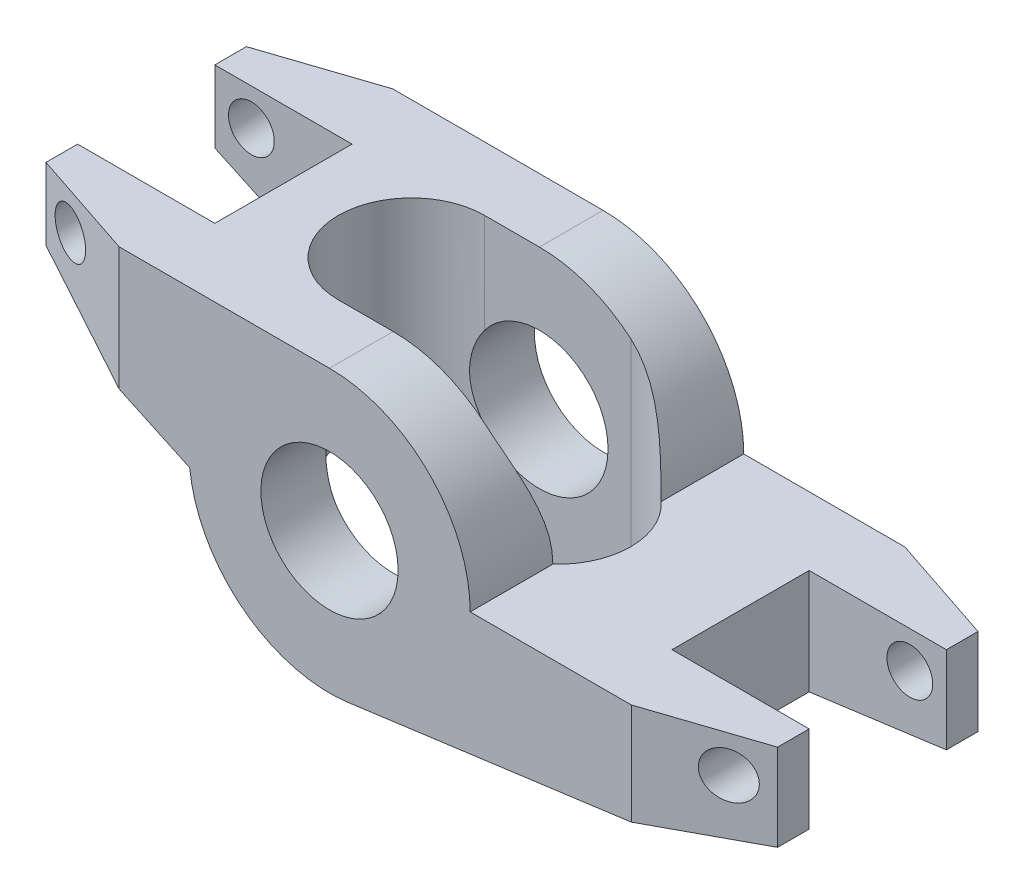
SolidWorks part; units mm, degrees
ref_plane "Front Plane" through (0, 0, 0) normal (0, 0, 1) x (1, 0, 0)
ref_plane "Top Plane" through (0, 0, 0) normal (0, 1, 0) x (1, 0, 0)
ref_plane "Right Plane" through (0, 0, 0) normal (1, 0, 0) x (0, 0, -1)
sketch "Sketch1" plane through (0, 0, 0) normal (0, 0, 1) x (1, 0, 0)
  line L0 (0, 9.77) -> (-22.23, 9.77)
  line L1 (-22.23, 9.77) -> (-22.23, 4.77)
  line L2 (-22.23, 4.77) -> (-9.7115, -1.0675)
  line L3 (9.77, 0) -> (28.58, 0)
  line L4 (28.58, 0) -> (28.58, -6.0277)
  line L5 (28.58, -6.0277) -> (1.2975, -9.6835)
  arc A0 (-9.7115, -1.0675) -> (1.2975, -9.6835) centre (0, 0) ccw
  circle A1 centre (0, 0) radius 4.765
  arc A2 (9.77, 0) -> (0, 9.77) centre (0, 0) ccw
  dimension "D1" = 19.54
  dimension "D2" = 9.53
  dimension "D3" = 5
  dimension "D4" = 25
  dimension "D5" = 22.23
  dimension "D6" = 28.58
extrude "Boss-Extrude2" add sketch "Sketch1" along normal mid plane 19
chamfer "Chamfer1" distance 2.54 distance2 7.62 2 edges at (28.58, -3.0139, 9.5) (-22.23, 7.27, 9.5)
chamfer "Chamfer2" distance 7.62 distance2 2.54 2 edges at (28.58, -3.0139, -9.5) (-22.23, 7.27, -9.5)
sketch "Sketch3" plane through (0, 9.77, 0) normal (0, 1, 0) x (1, 0, 0)
  line L0 (-22.23, -6.96) -> (-22.23, 6.96) construction
  line L1 (-22.23, 4.765) -> (-12.7, 4.765)
  line L2 (-22.23, 4.765) -> (-22.23, -4.765)
  line L3 (-22.23, -4.765) -> (-12.7, -4.765)
  line L4 (-12.7, 4.765) -> (-12.7, -4.765)
  line L5 (28.58, -6.96) -> (28.58, 6.96) construction
  line L6 (28.58, 4.765) -> (19.05, 4.765)
  line L7 (28.58, 4.765) -> (28.58, -4.765)
  line L8 (28.58, -4.765) -> (19.05, -4.765)
  line L9 (19.05, 4.765) -> (19.05, -4.765)
  point P12 (-12.7, 0)
  point P13 (19.05, 0)
  dimension "D1" = 9.53
extrude "Cut-Extrude1" cut sketch "Sketch3" against normal through all
sketch "Sketch4" plane through (0, 0, 0) normal (0, 1, 0) x (1, 0, 0)
  line L0 (-3.81, 0) -> (6.35, 0) construction
  line L1 (-3.81, 5.08) -> (6.35, 5.08)
  line L2 (-3.81, -5.08) -> (6.35, -5.08)
  line L3 (-12.7, -4.765) -> (-12.7, 4.765) construction
  arc A0 (-3.81, 5.08) -> (-3.81, -5.08) centre (-3.81, 0) ccw
  arc A1 (6.35, -5.08) -> (6.35, 5.08) centre (6.35, 0) ccw
  point P3 (1.27, 0)
  point P8 (0, 0)
  dimension "D2" = 5.08
  dimension "D1" = 8.89
  dimension "D3" = 10.16
extrude "Cut-Extrude2" cut sketch "Sketch4" against normal through all both and the other way through all
sketch "Sketch5" plane through (0, 0, 0) normal (0, 0, 1) x (1, 0, 0)
  line L0 (-22.23, 4.77) -> (-22.23, 9.77) construction
  line L1 (-22.23, 9.77) -> (-14.61, 9.77) construction
  line L2 (20.96, 0) -> (28.58, 0) construction
  line L3 (28.58, 0) -> (28.58, -6.0277) construction
  circle A0 centre (-19.69, 7.23) radius 1.59
  circle A1 centre (26.04, -2.54) radius 1.59
  point P6 (-22.23, 7.27)
  point P7 (0, 0)
  point P8 (0, 0)
  dimension "D1" = 3.18
  dimension "D2" = 2.54
  dimension "D3" = 2.54
  dimension "D4" = 2.54
  dimension "D5" = 2.54
extrude "Cut-Extrude3" cut sketch "Sketch5" against normal through all both and the other way through all
